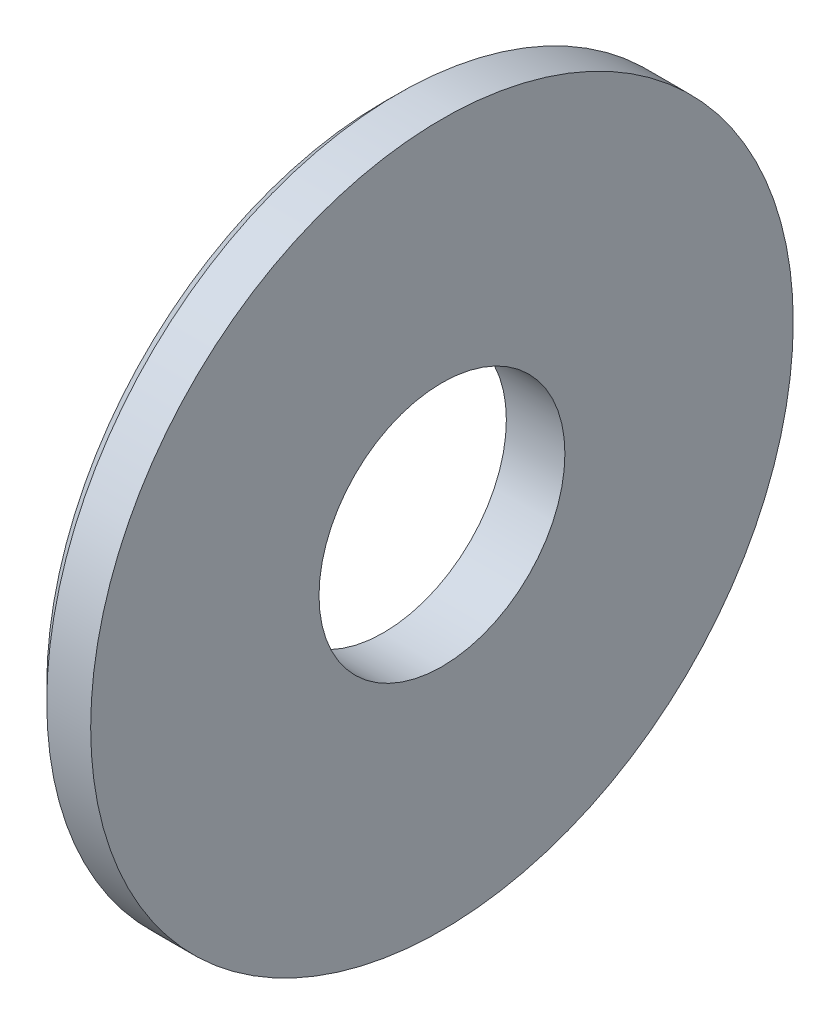
SolidWorks part; units mm, degrees
ref_plane "Alzado" through (0, 0, 0) normal (0, 0, 1) x (1, 0, 0)
ref_plane "Planta" through (0, 0, 0) normal (0, 1, 0) x (1, 0, 0)
ref_plane "Vista lateral" through (0, 0, 0) normal (1, 0, 0) x (0, 0, -1)
ref_plane "Plano1" through (0, 0, 0) normal (0, 0, -1) x (-1, 0, 0)
sketch "Croquis1" plane through (0, 0, 0) normal (0, 0, -1) x (-1, 0, 0)
  line L0 (0, 4.2) -> (0, 12)
  line L1 (0, 12) -> (-2, 12)
  line L2 (-2, 12) -> (-2, 4.2)
  line L3 (-2, 4.2) -> (0, 4.2)
  line L4 (-2, 0) -> (0, 0) construction
revolve "Revolución1" add sketch "Croquis1" angle 360 about L4
chamfer "Chaflán1" distance 0.5 angle 45 1 edges at (0, 0, 12)
